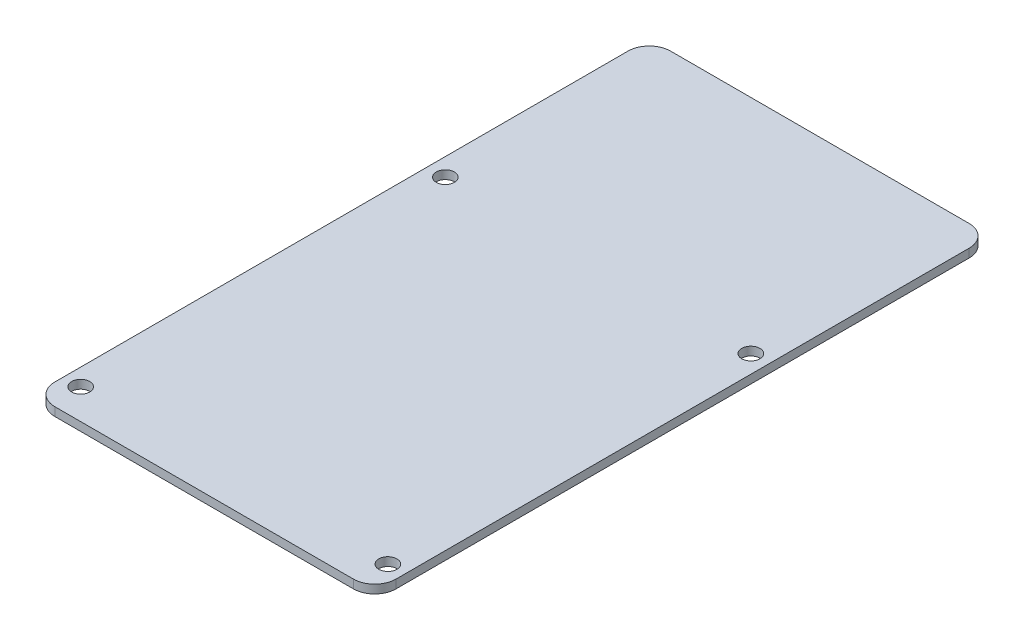
SolidWorks part; units mm, degrees
ref_plane "Front Plane" through (0, 0, 0) normal (1, 0, 0) x (0, 1, 0)
ref_plane "Top Plane" through (0, 0, 0) normal (0, 0, 1) x (0, 1, 0)
ref_plane "Right Plane" through (0, 0, 0) normal (0, 1, 0) x (-1, 0, 0)
sketch "Sketch1" plane through (0, 0, 0) normal (0, 1, 0) x (-1, 0, 0)
  line L0 (44.0418, -68.0583) -> (44.0418, 66.3054)
  line L1 (39.0418, 71.3054) -> (-30.9582, 71.3054)
  line L2 (-35.9582, 66.3054) -> (-35.9582, -68.0583)
  line L3 (-30.9582, -73.0583) -> (39.0418, -73.0583)
  arc A0 (39.0418, -73.0583) -> (44.0418, -68.0583) centre (39.0418, -68.0583) ccw
  arc A1 (44.0418, 66.3054) -> (39.0418, 71.3054) centre (39.0418, 66.3054) ccw
  arc A2 (-30.9582, 71.3054) -> (-35.9582, 66.3054) centre (-30.9582, 66.3054) ccw
  arc A3 (-35.9582, -68.0583) -> (-30.9582, -73.0583) centre (-30.9582, -68.0583) ccw
  circle A4 centre (-31.7679, -21.0583) radius 2.125
  circle A5 centre (39.8514, -21.0583) radius 2.125
  circle A6 centre (40.0418, 64.2271) radius 2.125
  circle A7 centre (-31.9582, 64.2271) radius 2.125
extrude "Boss-Extrude1" add sketch "Sketch1" along normal blind 2
